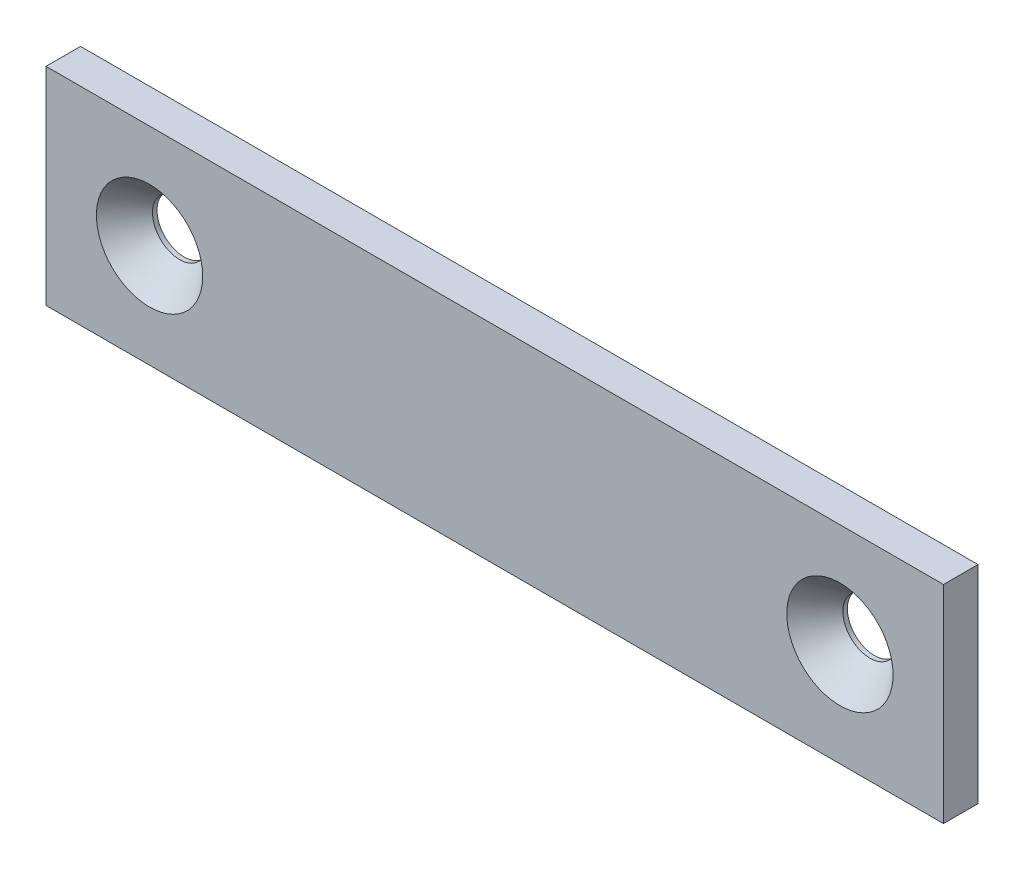
SolidWorks part; units mm, degrees
material "Delrin (Acetal)"
ref_plane "Front Plane" through (0, 0, 0) normal (0, 0, 1) x (1, 0, 0)
ref_plane "Top Plane" through (0, 0, 0) normal (0, 1, 0) x (1, 0, 0)
ref_plane "Right Plane" through (0, 0, 0) normal (1, 0, 0) x (0, 0, -1)
sketch "Sketch1" plane through (0, 0, 0) normal (0, 0, 1) x (1, 0, 0)
  line L1 (-41.275, 9.525) -> (41.275, 9.525)
  line L2 (-41.275, 9.525) -> (-41.275, -9.525)
  line L3 (-41.275, -9.525) -> (41.275, -9.525)
  line L4 (41.275, 9.525) -> (41.275, -9.525)
  point P4 (0, 9.525)
  point P6 (-41.275, 0)
  dimension "D1" = 82.55
  dimension "D2" = 19.05
extrude "Extrude1" add sketch "Sketch1" along normal mid plane 3.175
hole_wizard "CSK for #10 Flat Head Machine Screw1" positions "Sketch3" profile "Sketch2" countersink size "#10" standard "Ansi Inch" end condition through all
sketch "Sketch3" plane through (0, 0, 1.5875) normal (0, 0, 1) x (1, 0, 0)
  line L0 (-31.75, 0) -> (31.75, 0) construction
  point P0 (-31.75, 0)
  point P1 (31.75, 0)
  point P6 (0, 0)
  dimension "D1" = 63.5
sketch "Sketch2" plane through (-31.75, 0, 1.5875) normal (1, 0, 0) x (0, -1, 0)
  line L0 (0, 0) -> (0, 3.175)
  line L1 (0, 3.175) -> (2.4892, 3.175)
  line L2 (2.4892, 3.175) -> (2.4892, 2.7612)
  line L3 (2.4892, 2.7612) -> (4.8895, 0)
  line L5 (4.8895, 0) -> (0, 0)
  line L6 (-2.4892, 2.7612) -> (-4.8895, 0) construction
  line L11 (0, -6.35) -> (0, 107.95) construction
  dimension "Thru Hole Dia." = 4.9784
  dimension "Thru Hole Depth" = 3.175
  dimension "Near C'Sink Dia." = 9.779
  dimension "Near C'Sink Angle" = 82
